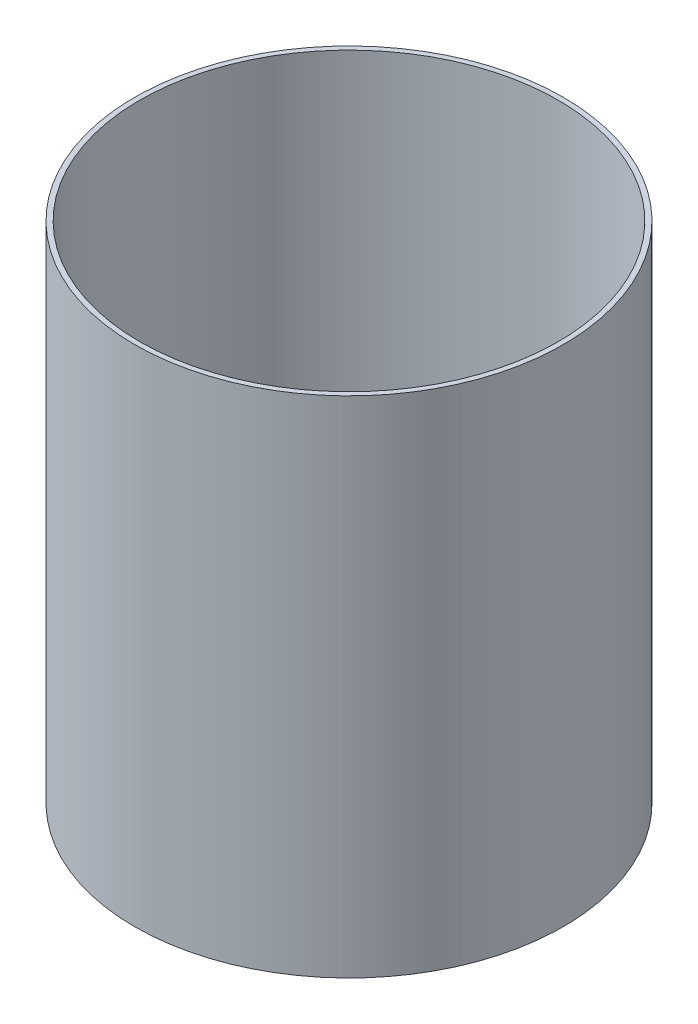
SolidWorks part; units mm, degrees
ref_plane "Front Plane" through (0, 0, 0) normal (0, 0, 1) x (1, 0, 0)
ref_plane "Top Plane" through (0, 0, 0) normal (0, 1, 0) x (1, 0, 0)
ref_plane "Right Plane" through (0, 0, 0) normal (1, 0, 0) x (0, 0, -1)
sketch "Sketch1" plane through (0, 0, 0) normal (0, 1, 0) x (1, 0, 0)
  circle A0 centre (0, 0) radius 21.082
  circle A1 centre (0, 0) radius 21.59
  dimension "D1" = 42.164
  dimension "D2" = 0.508
extrude "Boss-Extrude1" add sketch "Sketch1" along normal blind 50.8
